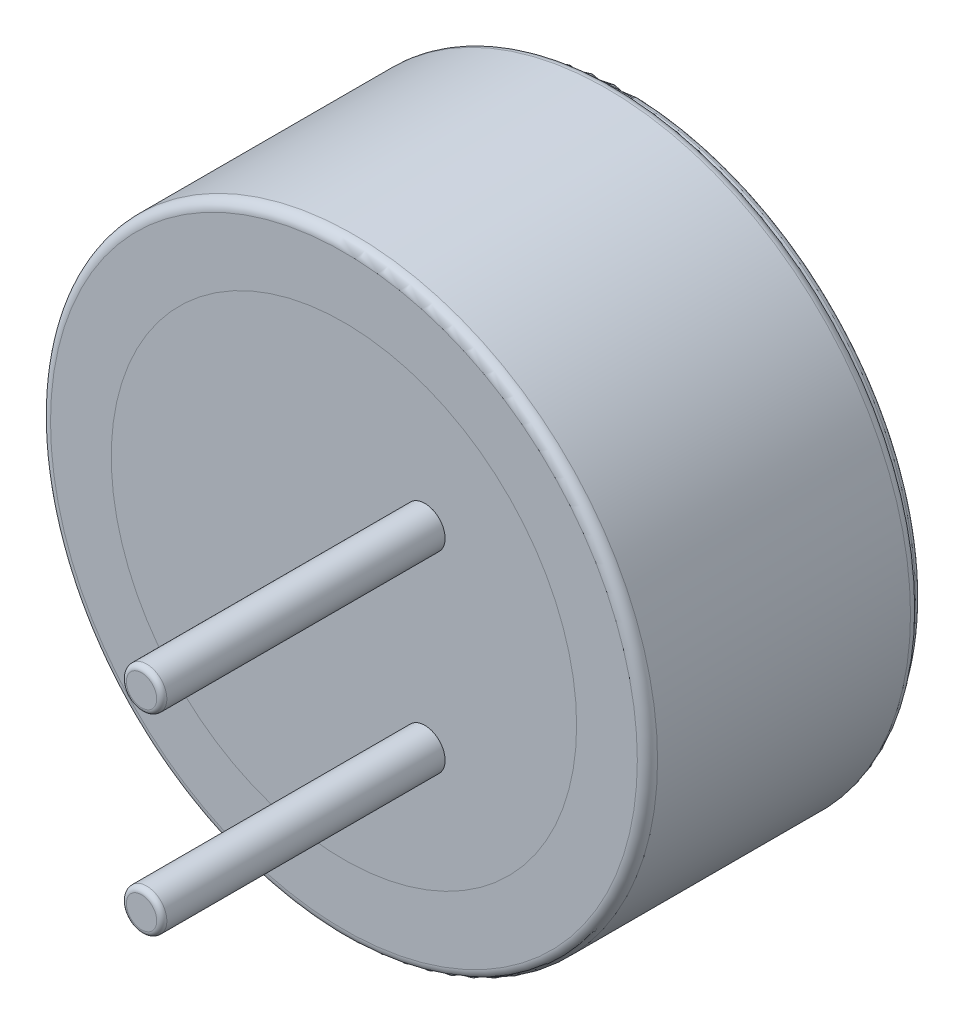
SolidWorks part; units mm, degrees
ref_plane "Front Plane" through (0, 0, 0) normal (0, 0, 1) x (1, 0, 0)
ref_plane "Top Plane" through (0, 0, 0) normal (0, 1, 0) x (1, 0, 0)
ref_plane "Right Plane" through (0, 0, 0) normal (1, 0, 0) x (0, 0, -1)
sketch "Sketch1" plane through (0, 0, 0) normal (0, 0, 1) x (1, 0, 0)
  circle A0 centre (0, 0) radius 3
  dimension "D1" = 6
extrude "Boss-Extrude1" add sketch "Sketch1" along normal blind 2.7
sketch "Sketch3" plane through (0, 0, 2.7) normal (0, 0, 1) x (1, 0, 0)
  line L0 (0, 3.186) -> (0, -3.2594) construction
  line L1 (-3.288, 0) -> (3.3125, 0) construction
  circle A0 centre (0.8, -0.95) radius 0.2
  circle A1 centre (0.8, 0.95) radius 0.2
  dimension "D1" = 0.4
  dimension "D2" = 0.8
  dimension "D3" = 0.95
extrude "Boss-Extrude2" add sketch "Sketch3" along normal blind 2.8 separate body
fillet "Fillet1" radius 0.1 2 edges at (3, 0, 2.7) (3, 0, 0)
sketch "Sketch4" plane through (0, 0, 0) normal (0, 0, -1) x (-1, 0, 0)
  circle A0 centre (0, 0) radius 2.9
  circle A1 centre (0, 0) radius 2.9 construction
extrude "Boss-Extrude3" add sketch "Sketch4" along normal blind 0.1 separate body
fillet "Fillet2" radius 0.05 1 edges at (-2.9, 0, -0.1)
sketch "Sketch6" plane through (0, 0, 2.7) normal (0, 0, 1) x (1, 0, 0)
  circle A0 centre (0, 0) radius 2.3
  dimension "D1" = 4.6
extrude "Cut-Extrude1" cut sketch "Sketch6" against normal blind 0.1
sketch "Sketch7" plane through (0, 0, 2.6) normal (0, 0, 1) x (1, 0, 0)
  circle A0 centre (0, 0) radius 2.3
  circle A1 centre (0, 0) radius 2.3 construction
extrude "Boss-Extrude6" add sketch "Sketch7" along normal blind 0.1 separate body
fillet "Fillet3" radius 0.05 1 edges at (1, -0.95, 5.5)
fillet "Fillet4" radius 0.05 1 edges at (0.6, 0.95, 5.5)
